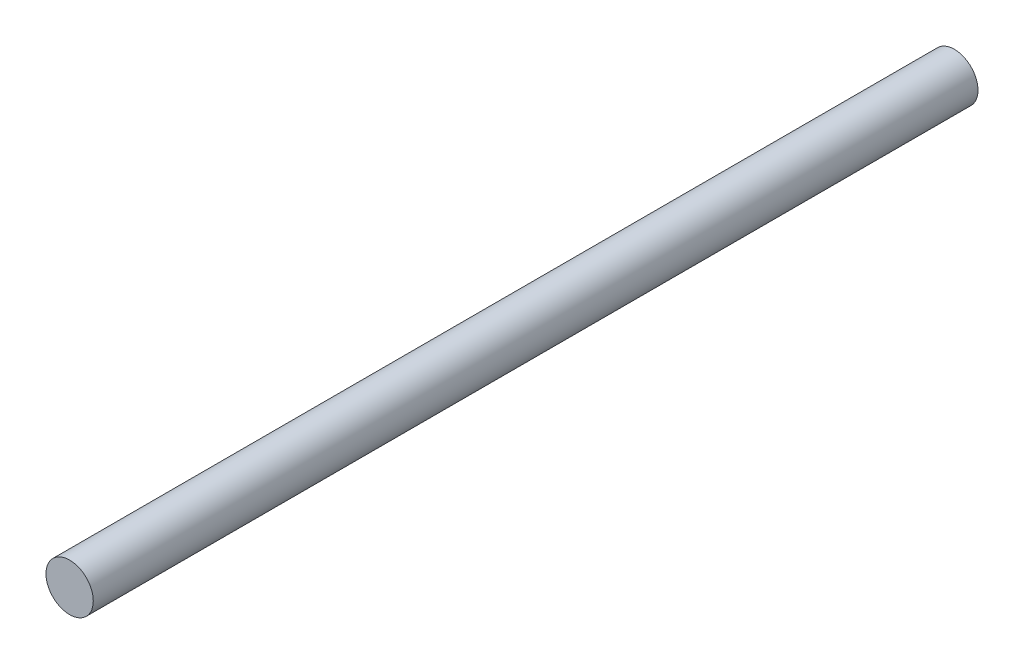
SolidWorks part; units mm, degrees
ref_plane "Front Plane" through (0, 0, 0) normal (0, 0, 1) x (1, 0, 0)
ref_plane "Top Plane" through (0, 0, 0) normal (0, 1, 0) x (1, 0, 0)
ref_plane "Right Plane" through (0, 0, 0) normal (1, 0, 0) x (0, 0, -1)
sketch "Sketch1" plane through (0, 0, 0) normal (0, 0, 1) x (1, 0, 0)
  circle A0 centre (0, 0) radius 11.5
  dimension "D1" = 23
extrude "Boss-Extrude1" add sketch "Sketch1" along normal mid plane 430
